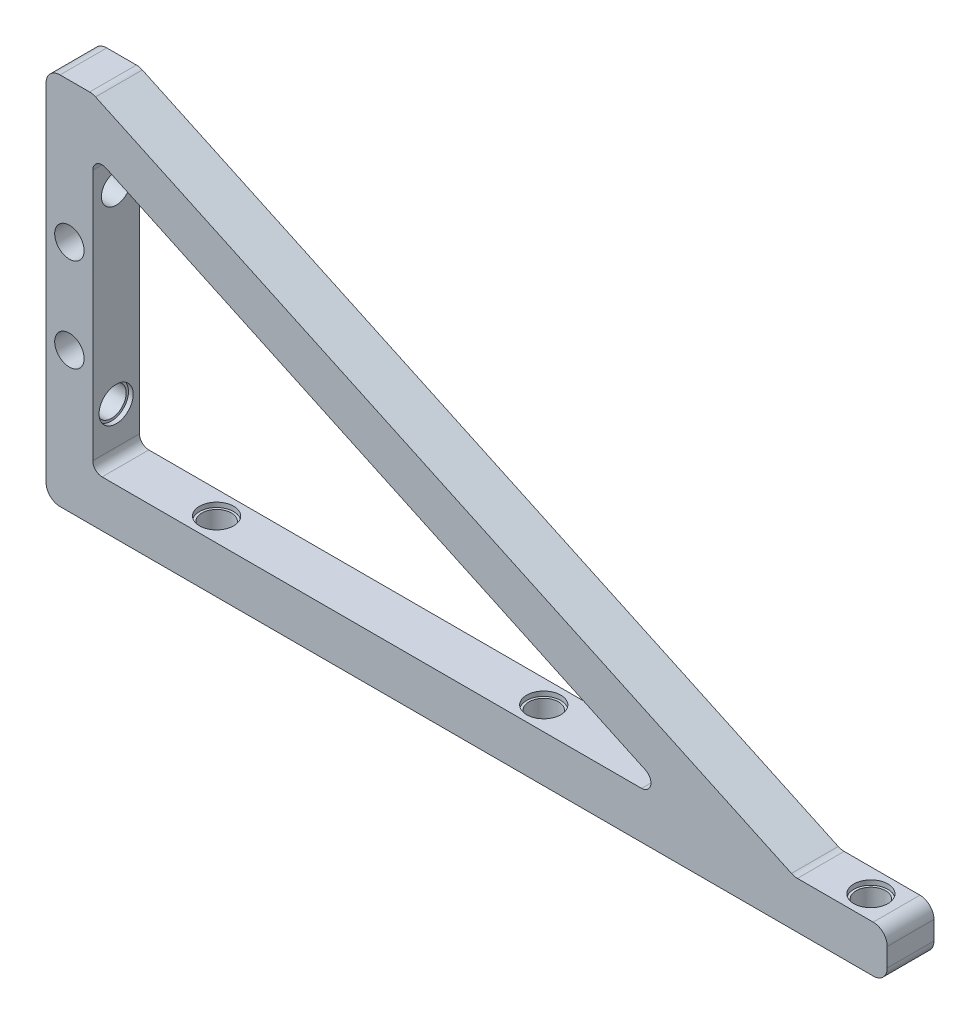
SolidWorks part; units mm, degrees
ref_plane "Plan de face" through (0, 0, 0) normal (0, 0, 1) x (1, 0, 0)
ref_plane "Plan de dessus" through (0, 0, 0) normal (0, 1, 0) x (1, 0, 0)
ref_plane "Plan de droite" through (0, 0, 0) normal (1, 0, 0) x (0, 0, -1)
sketch "Esquisse1" plane through (0, 0, 0) normal (0, 0, 1) x (1, 0, 0)
  line L1 (0, 0) -> (180, 0)
  line L2 (0, 0) -> (0, 80)
  line L3 (0, 80) -> (180, 80)
  line L4 (180, 0) -> (180, 80)
  dimension "D1" = 180
  dimension "D2" = 80
extrude "Boss.-Extru.1" add sketch "Esquisse1" along normal blind 10
sketch "Esquisse2" plane through (0, 0, 10) normal (0, 0, 1) x (1, 0, 0)
  line L0 (180, 80) -> (0, 80) construction
  line L1 (10, 80) -> (180, 80)
  line L2 (10, 80) -> (10, 10)
  line L3 (10, 10) -> (180, 10)
  line L4 (180, 80) -> (180, 10)
  line L5 (180, 0) -> (180, 80) construction
  line L6 (0, 0) -> (180, 0) construction
  line L7 (0, 80) -> (0, 0) construction
  dimension "D1" = 10
  dimension "D2" = 10
extrude "Enlèv. mat.-Extru.1" cut sketch "Esquisse2" against normal through all both and the other way through all
sketch "Esquisse3" plane through (0, 0, 10) normal (0, 0, 1) x (1, 0, 0)
  line L0 (10, 80) -> (160.1155, 10)
  line L1 (180, 10) -> (10, 10) construction
  line L2 (160.1155, 10) -> (136.4535, 10)
  line L3 (136.4535, 10) -> (10, 68.9662)
  line L4 (10, 10) -> (10, 80) construction
  line L5 (10, 68.9662) -> (10, 80)
  dimension "D1" = 25
  dimension "D2" = 10
extrude "Boss.-Extru.2" add sketch "Esquisse3" against normal up to vertex (10 mm away)
sketch "Esquisse4" plane through (0, 0, 0) normal (0, -1, 0) x (1, 0, 0)
  line L0 (0, 5) -> (180, 5) construction
  line L1 (0, 10) -> (0, 0) construction
  line L2 (180, 10) -> (180, 0) construction
  line L3 (101.5, 5) -> (101.5, 0) construction
  line L5 (0, 0) -> (180, 0) construction
  circle A0 centre (101.5, 5) radius 3.15
  circle A1 centre (171.5, 5) radius 3.15
  circle A2 centre (31.5, 5) radius 3.15
  dimension "D1" = 6.3
  dimension "D2" = 70
  dimension "D3" = 101.5
extrude "Enlèv. mat.-Extru.2" cut sketch "Esquisse4" against normal up to next and the other way through all
sketch "Esquisse5" plane through (0, 10, 0) normal (0, 1, 0) x (1, 0, 0)
  line L1 (101.5, -5) -> (101.5, -10) construction
  line L2 (180, -10) -> (160.1155, -10) construction
  circle A0 centre (101.5, -5) radius 3.65
  circle A1 centre (171.5, -5) radius 3.65
  circle A2 centre (31.5, -5) radius 3.65
  dimension "D1" = 7.3
extrude "Enlèv. mat.-Extru.3" cut sketch "Esquisse5" against normal blind 1
sketch "Esquisse6" plane through (0, 0, 0) normal (-1, 0, 0) x (0, 0, 1)
  line L0 (5, 80) -> (5, 0) construction
  line L1 (10, 80) -> (0, 80) construction
  line L2 (10, 0) -> (0, 0) construction
  line L3 (5, 40) -> (10, 40) construction
  line L4 (10, 80) -> (10, 0) construction
  circle A0 centre (5, 60) radius 3.15
  circle A1 centre (5, 20) radius 3.15
  dimension "D1" = 6.3
  dimension "D2" = 40
extrude "Enlèv. mat.-Extru.4" cut sketch "Esquisse6" against normal up to next and the other way through all
sketch "Esquisse7" plane through (0, 0, 0) normal (-1, 0, 0) x (0, 0, 1)
  circle A0 centre (5, 60) radius 3.65
  dimension "D1" = 7.3
extrude "Enlèv. mat.-Extru.5" cut sketch "Esquisse7" against normal blind 1
sketch "Esquisse8" plane through (10, 0, 0) normal (1, 0, 0) x (0, 0, -1)
  circle A0 centre (-5, 20) radius 3.65
  dimension "D1" = 7.3
extrude "Enlèv. mat.-Extru.6" cut sketch "Esquisse8" against normal blind 1
fillet "Congé1" radius 2 3 edges at (10, 10, 5) (136.4535, 10, 5) (10, 68.9662, 5)
fillet "Congé2" radius 3 6 edges at (160.1155, 10, 5) (180, 10, 5) (180, 0, 5) (0, 0, 5) (10, 80, 5) (0, 80, 5)
sketch "Esquisse9" plane through (0, 0, 10) normal (0, 0, 1) x (1, 0, 0)
  line L0 (0, 30) -> (10, 30) construction
  line L1 (0, 77) -> (0, 3) construction
  line L2 (10, 12) -> (10, 65.8268) construction
  line L3 (5, 30) -> (5, 50) construction
  line L4 (3, 0) -> (177, 0) construction
  circle A0 centre (5, 50) radius 3.15
  circle A1 centre (5, 30) radius 3.15
  dimension "D1" = 6.3
  dimension "D2" = 20
  dimension "D3" = 30
extrude "Enlèv. mat.-Extru.7" cut sketch "Esquisse9" against normal through all both and the other way through all
sketch "Esquisse10" plane through (0, 0, 10) normal (0, 0, 1) x (1, 0, 0)
  circle A0 centre (5, 50) radius 3.65
  circle A1 centre (5, 30) radius 3.65
  dimension "D1" = 7.3
extrude "Enlèv. mat.-Extru.8" cut sketch "Esquisse10" along normal blind 1 from surface at -10 starting at face at (8.15, 30, 0)
